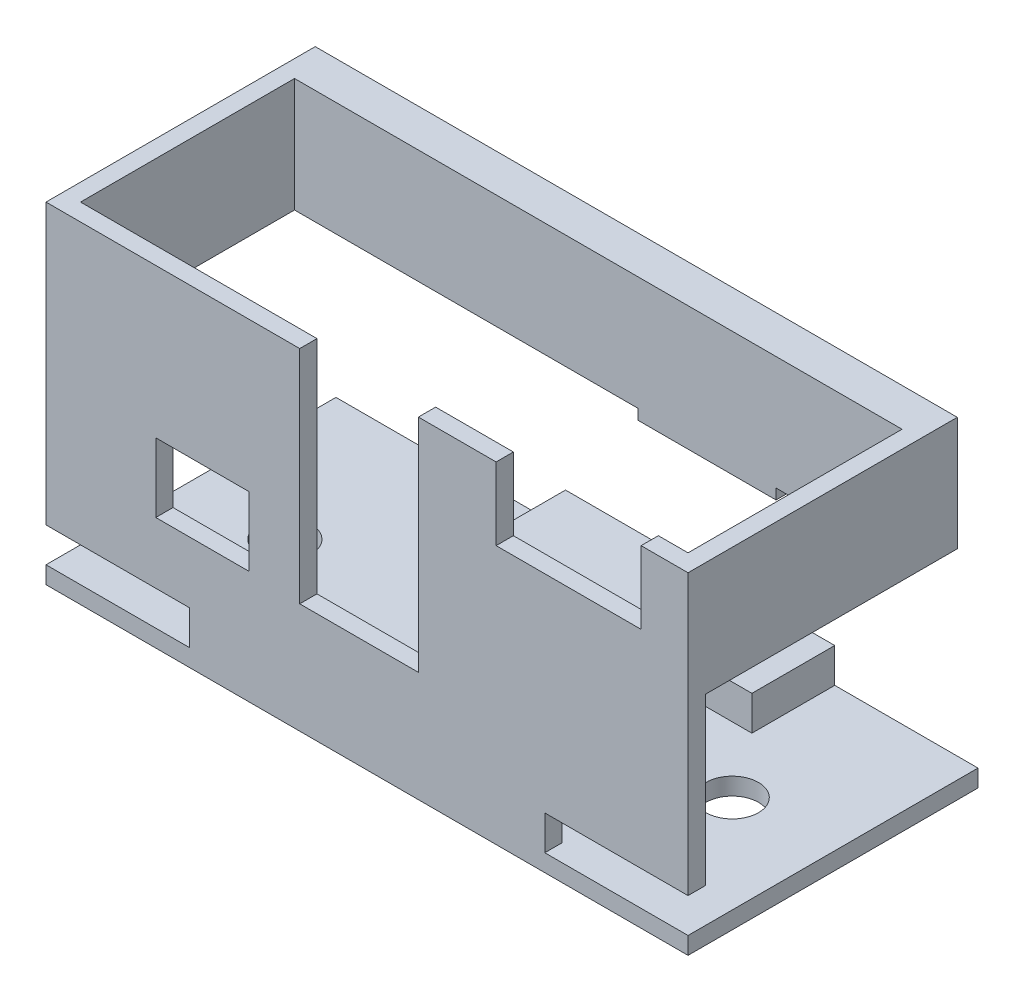
SolidWorks part; units mm, degrees
ref_plane "Front" through (0, 0, 0) normal (0, 0, 1) x (1, 0, 0)
ref_plane "Top" through (0, 0, 0) normal (0, 1, 0) x (1, 0, 0)
ref_plane "Right" through (0, 0, 0) normal (1, 0, 0) x (0, 0, -1)
sketch "Sketch1" plane through (0, 0, 0) normal (0, 0, 1) x (1, 0, 0)
  line L0 (-1.25, 0) -> (-1.25, 24)
  line L1 (-1.25, 0) -> (45.25, 0)
  line L2 (0, 0) -> (0, 22.75) construction
  line L3 (-1.25, 22.75) -> (45.25, 22.75) construction
  line L4 (44, 0) -> (44, 22.75) construction
  line L5 (45.25, 0) -> (45.25, 24)
  line L6 (-1.25, 24) -> (45.25, 24)
  line L7 (-1.25, 0) -> (-1.25, 22.75) construction
  line L8 (45.25, 0) -> (45.25, 22.75) construction
  dimension "D1" = 44
  dimension "D2" = 22.75
  dimension "D5" = 46.5
  dimension "D3" = 1.25
  dimension "D4" = 1.25
  dimension "D6" = 1.25
extrude "Boss-Extrude1" add sketch "Sketch1" against normal blind 21
shell "Shell1" thickness 1.25
sketch "Sketch2" plane through (-1.25, 0, 0) normal (-1, 0, 0) x (0, 0, 1)
  line L0 (-1.25, 24) -> (-1.25, 1.25) construction
  line L1 (-21, 1.25) -> (-1.25, 1.25)
  line L2 (-21, 1.25) -> (-21, 15.75)
  line L3 (-21, 15.75) -> (-1.25, 15.75)
  line L4 (-1.25, 1.25) -> (-1.25, 15.75)
  dimension "D1" = 14.5
extrude "Cut-Extrude1" cut sketch "Sketch2" against normal through all
sketch "Sketch6" plane through (0, 0, 0) normal (0, -1, 0) x (-1, 0, 0)
  circle A0 centre (-38.2, 10.25) radius 2.875 construction
  circle A1 centre (-5.8, 10.25) radius 4.25 construction
  circle A2 centre (-5.8, 10.25) radius 4.25 construction
  circle A4 centre (-5.8, 10.25) radius 1.75 construction
  circle A5 centre (-5.8, 10.25) radius 1.75 construction
  circle A6 centre (-5.8, 10.25) radius 1.9
  circle A7 centre (-38.2, 10.25) radius 2.875 construction
  circle A8 centre (-38.2, 10.25) radius 1.75 construction
  circle A9 centre (-38.2, 10.25) radius 1.9
  circle A10 centre (-38.2, 10.25) radius 1.75 construction
  dimension "D1" = 0.15
  dimension "D3" = 0.15
sketch "Sketch7" plane through (0, 0, 0) normal (0, 0, 1) x (1, 0, 0)
  line L0 (45.25, 0) -> (45.25, 24) construction
  line L1 (45.25, 1.25) -> (34.875, 1.25)
  line L2 (45.25, 1.25) -> (45.25, 3.75)
  line L3 (45.25, 3.75) -> (34.875, 3.75)
  line L4 (34.875, 1.25) -> (34.875, 3.75)
  line L5 (-1.25, 0) -> (45.25, 0) construction
  line L7 (35.925, 0) -> (39.825, 0) construction
  line L8 (37.875, 0) -> (37.875, 1.5787) construction
  line L9 (22, 0) -> (22, 4.652) construction
  line L10 (9.125, 1.25) -> (9.125, 3.75)
  line L11 (-1.25, 3.75) -> (9.125, 3.75)
  line L12 (-1.25, 1.25) -> (-1.25, 3.75)
  line L13 (-1.25, 1.25) -> (9.125, 1.25)
  dimension "D1" = 1.25
  dimension "D2" = 3
  dimension "D3" = 2.5
extrude "Cut-Extrude5" cut sketch "Sketch7" against normal up to surface (1.25 mm away) up to face at (22, 14.1875, -1.25)
sketch "Sketch9" plane through (0, 1.25, 0) normal (0, 1, 0) x (1, 0, 0)
  line L0 (-1.25, 21) -> (45.25, 21) construction
  line L1 (34.875, 21) -> (15.375, 21)
  line L2 (34.875, 21) -> (34.875, 15)
  line L3 (34.875, 15) -> (15.375, 15)
  line L4 (15.375, 21) -> (15.375, 15)
  line L6 (34.875, 1.25) -> (34.875, 21) construction
  dimension "D1" = 6
  dimension "D2" = 19.5
extrude "Boss-Extrude3" add sketch "Sketch9" along normal blind 2.5
sketch "Sketch12" plane through (45.25, 0, 0) normal (1, 0, 0) x (0, 0, -1)
  line L1 (1.25, 15.75) -> (21, 15.75) construction
  line L2 (21, 24) -> (19.5, 24)
  line L3 (21, 24) -> (21, 15.75)
  line L4 (21, 15.75) -> (19.5, 15.75)
  line L5 (19.5, 24) -> (19.5, 15.75)
  dimension "D1" = 1.5
extrude "Cut-Extrude7" cut sketch "Sketch12" along normal through all and the other way through all from surface at -45.25 starting at face at (0, 19.875, -11.125)
sketch "Sketch13" plane through (0, 0, 0) normal (1, 0, 0) x (0, 0, -1)
  line L0 (1.25, 15.75) -> (19.5, 15.75) construction
  line L1 (19.5, 24) -> (16.75, 24)
  line L2 (19.5, 24) -> (19.5, 15.75)
  line L3 (19.5, 15.75) -> (16.75, 15.75)
  line L4 (16.75, 24) -> (16.75, 15.75)
  dimension "D1" = 2.75
extrude "Boss-Extrude4" add sketch "Sketch13" along normal up to vertex (44 mm away) contours L4 L3 L2 L1
sketch "Sketch15" plane through (0, 15.75, 0) normal (0, -1, 0) x (1, 0, 0)
  line L0 (-1.25, -19.5) -> (45.25, -19.5) construction
  line L1 (34.875, -19.5) -> (24.875, -19.5)
  line L2 (34.875, -19.5) -> (34.875, -16.75)
  line L3 (34.875, -16.75) -> (24.875, -16.75)
  line L4 (24.875, -19.5) -> (24.875, -16.75)
  line L5 (44, -16.75) -> (0, -16.75) construction
  line L6 (34.875, -15) -> (34.875, -21) construction
  dimension "D1" = 10
extrude "Boss-Extrude5" add sketch "Sketch15" along normal blind 0.75 contours L1 L4 L3 L2
sketch "Sketch17" plane through (0, 0, -2.75) normal (0, 0, 1) x (1, 0, 0)
  line L4 (8.2, 9.19) -> (11.96, 9.19)
  line L5 (8.2, 12.19) -> (8.2, 9.19)
  line L6 (11.96, 12.19) -> (8.2, 12.19)
  line L7 (11.96, 9.19) -> (11.96, 12.19)
  line L8 (8.2, 9.19) -> (11.96, 9.19)
  line L9 (8.2, 12.19) -> (8.2, 9.19)
  line L10 (11.96, 12.19) -> (8.2, 12.19)
  line L11 (11.96, 9.19) -> (11.96, 12.19)
  line L12 (19.1256, 9.4882) -> (23.7194, 9.4882)
  line L13 (23.7194, 9.4882) -> (23.7194, 14.357)
  line L14 (23.7194, 14.357) -> (19.1256, 14.357)
  line L15 (19.1256, 14.357) -> (19.1256, 9.4882)
  line L16 (19.1256, 9.4882) -> (23.7194, 9.4882)
  line L17 (23.7194, 9.4882) -> (23.7194, 14.357)
  line L18 (23.7194, 14.357) -> (19.1256, 14.357)
  line L19 (19.1256, 14.357) -> (19.1256, 9.4882)
  dimension "D1" = 0
  dimension "D2" = 0
sketch "Sketch18" plane through (0, 0, 0) normal (0, 0, 1) x (1, 0, 0)
  line L0 (8.2, 12.19) -> (8.2, 9.19) construction
  line L1 (6.7, 13.19) -> (13.46, 13.19)
  line L2 (6.7, 13.19) -> (6.7, 8.19)
  line L3 (6.7, 8.19) -> (13.46, 8.19)
  line L4 (13.46, 13.19) -> (13.46, 8.19)
  line L5 (11.96, 12.19) -> (8.2, 12.19) construction
  line L6 (11.96, 9.19) -> (11.96, 12.19) construction
  line L7 (8.2, 9.19) -> (11.96, 9.19) construction
  dimension "D1" = 1.5
  dimension "D2" = 1
  dimension "D3" = 1.5
  dimension "D4" = 1
extrude "Cut-Extrude8" cut sketch "Sketch18" against normal up to next
sketch "Sketch22" plane through (0, 0, 0) normal (0, 0, 1) x (1, 0, 0)
  line L0 (45.25, 24) -> (-1.25, 24) construction
  line L1 (17.1256, 24) -> (25.7194, 24)
  line L2 (17.1256, 24) -> (17.1256, 7.9882)
  line L3 (17.1256, 7.9882) -> (25.7194, 7.9882)
  line L4 (25.7194, 24) -> (25.7194, 7.9882)
  line L5 (19.1256, 14.357) -> (19.1256, 9.4882) construction
  line L6 (23.7194, 9.4882) -> (23.7194, 14.357) construction
  line L7 (19.1256, 9.4882) -> (23.7194, 9.4882) construction
  dimension "D1" = 2
  dimension "D2" = 2
  dimension "D3" = 1.5
extrude "Cut-Extrude9" cut sketch "Sketch22" against normal up to next
ref_plane "Plane1" through (41.175, 19.5, -0.25) normal (1, 0, 0) x (0, -1, 0)
sketch "Sketch25" plane through (0, 0, 0) normal (0, 0, 1) x (1, 0, 0)
  line L1 (41.85, 18.75) -> (31.35, 18.75)
  line L2 (41.85, 18.75) -> (41.85, 24)
  line L3 (41.85, 24) -> (31.35, 24)
  line L4 (31.35, 18.75) -> (31.35, 24)
  line L16 (17.1256, 7.9882) -> (17.1256, 24)
  line L17 (17.1256, 24) -> (-1.25, 24)
  line L18 (-1.25, 24) -> (-1.25, 3.75)
  line L23 (-1.25, 0) -> (45.25, 0)
  line L24 (45.25, 0) -> (45.25, 1.25)
  line L25 (-1.25, 3.75) -> (9.125, 3.75)
  line L26 (-1.25, 3.75) -> (9.125, 3.75)
  line L27 (9.125, 3.75) -> (9.125, 1.25)
  line L28 (9.125, 3.75) -> (9.125, 1.25)
  line L29 (45.25, 24) -> (25.7194, 24)
  line L30 (25.7194, 24) -> (25.7194, 7.9882)
  line L31 (25.7194, 7.9882) -> (17.1256, 7.9882)
  line L32 (17.1256, 7.9882) -> (17.1256, 24)
  line L33 (17.1256, 24) -> (-1.25, 24)
  line L34 (-1.25, 24) -> (-1.25, 3.75)
  line L35 (9.125, 1.25) -> (-1.25, 1.25)
  line L36 (9.125, 1.25) -> (-1.25, 1.25)
  line L37 (-1.25, 1.25) -> (-1.25, 0)
  line L38 (-1.25, 1.25) -> (-1.25, 0)
  line L39 (-1.25, 0) -> (45.25, 0)
  line L40 (45.25, 0) -> (45.25, 1.25)
  line L41 (45.25, 1.25) -> (34.875, 1.25)
  line L42 (45.25, 1.25) -> (34.875, 1.25)
  line L43 (34.875, 1.25) -> (34.875, 3.75)
  line L44 (34.875, 1.25) -> (34.875, 3.75)
  line L45 (45.25, 24) -> (25.7194, 24)
  line L46 (25.7194, 24) -> (25.7194, 7.9882)
  line L47 (25.7194, 7.9882) -> (17.1256, 7.9882)
  line L48 (34.875, 3.75) -> (45.25, 3.75)
  line L49 (34.875, 3.75) -> (45.25, 3.75)
  line L50 (45.25, 3.75) -> (45.25, 24)
  line L51 (45.25, 3.75) -> (45.25, 24)
  line L52 (31.6, 24) -> (31.6, 19.5)
  line L53 (31.6, 19.5) -> (41.6, 19.5)
  line L54 (41.6, 19.5) -> (41.6, 24)
  line L55 (41.6, 24) -> (31.6, 24)
  line L56 (31.6, 24) -> (31.6, 19.5)
  line L57 (31.6, 19.5) -> (41.6, 19.5)
  line L58 (41.6, 19.5) -> (41.6, 24)
  line L59 (41.6, 24) -> (31.6, 24)
  line M34 (45.25, 24) -> (25.7194, 24)
  dimension "D3" = 0.25
  dimension "D4" = 0.75
  dimension "D5" = 0.25
  dimension "D1" = 0
  dimension "D2" = 0
extrude "Cut-Extrude15" cut sketch "Sketch25" against normal up to next contours L58 L57 L56 L45 L4 L1 L2 M34 | L57 L58 L45 L56
extrude "Cut-Extrude16" cut sketch "Sketch6" against normal up to next
